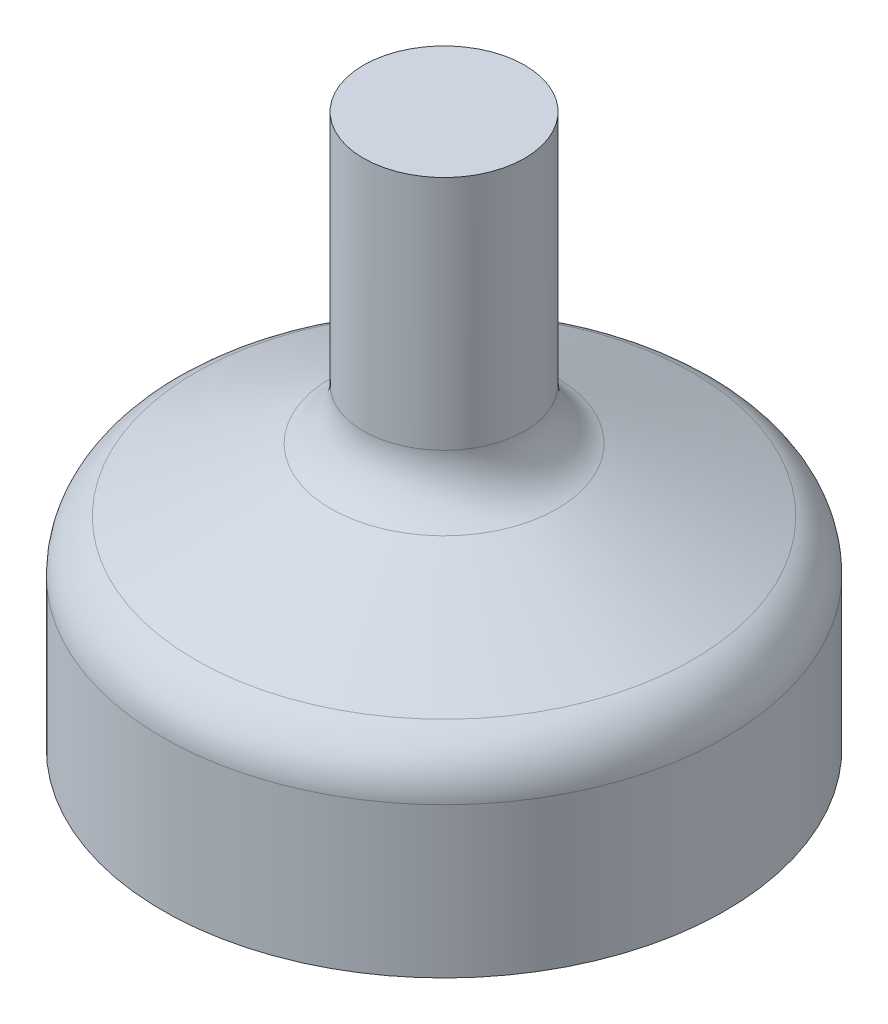
SolidWorks part; units mm, degrees
ref_plane "Front Plane" through (0, 0, 0) normal (0, 0, 1) x (1, 0, 0)
ref_plane "Top Plane" through (0, 0, 0) normal (0, 1, 0) x (1, 0, 0)
ref_plane "Right Plane" through (0, 0, 0) normal (1, 0, 0) x (0, 0, -1)
sketch "Sketch1" plane through (0, 0, 0) normal (0, 1, 0) x (1, 0, 0)
  circle A0 centre (0, 0) radius 3.75
  dimension "D1" = 7.5
ref_plane "Plane1" through (0, 6.2, 0) normal (0, 1, 0) x (1, 0, 0)
sketch "Sketch2" plane through (0, 6.2, 0) normal (0, 1, 0) x (1, 0, 0)
  circle A0 centre (0, 0) radius 1.075
  dimension "D1" = 2.15
sketch "Sketch6" plane through (0, 0, 0) normal (1, 0, 0) x (0, 0, -1)
  line L0 (-3.75, 0) -> (-3.75, 2)
  line L1 (-3.316, 2.6802) -> (-1.509, 3.5198)
  line L2 (-1.075, 4.2) -> (-1.075, 6.2)
  arc A0 (-1.075, 4.2) -> (-1.509, 3.5198) centre (-1.825, 4.2) cw
  arc A1 (-3.75, 2) -> (-3.316, 2.6802) centre (-3, 2) cw
  dimension "D2" = 2
  dimension "D3" = 2
sketch "Sketch7" plane through (0, 0, 0) normal (1, 0, 0) x (0, 0, -1)
  line L0 (0, -0.2276) -> (0, 2.526)
revolve "Revolve-Thin2" add sketch "Sketch6" angle 360 about L0
sketch "Sketch8" plane through (0, 6.2, 0) normal (0, 1, 0) x (1, 0, 0)
  circle A0 centre (0, 0) radius 1.075
  circle A2 centre (0, 0) radius 1.075 construction
extrude "Boss-Extrude1" add sketch "Sketch8" along normal blind 1.15
